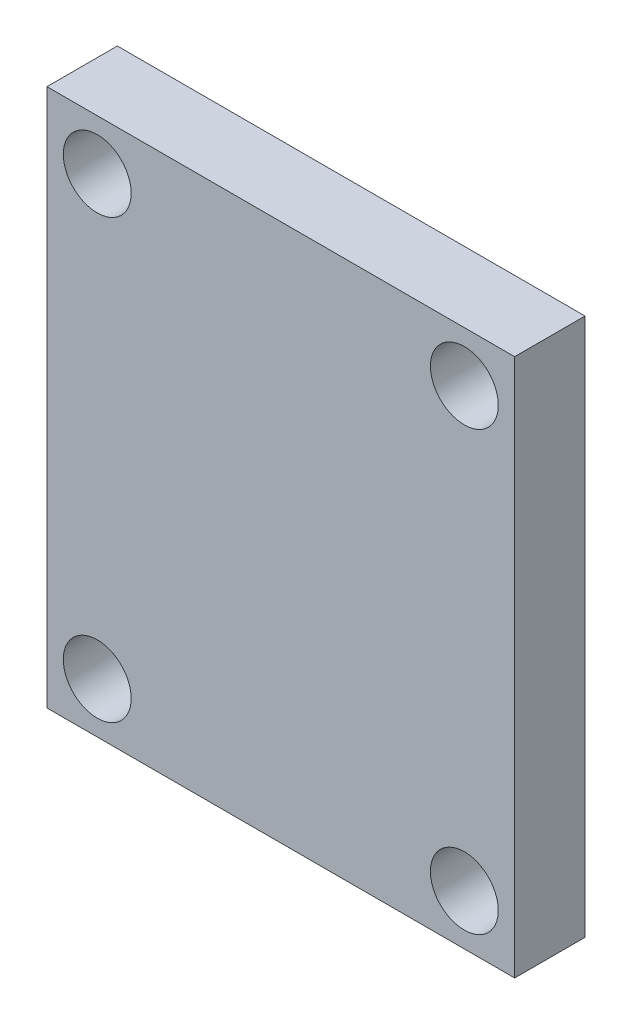
SolidWorks part; units mm, degrees
ref_plane "Přední rovina" through (0, 0, 0) normal (0, 0, 1) x (1, 0, 0)
ref_plane "Horní rovina" through (0, 0, 0) normal (0, 1, 0) x (1, 0, 0)
ref_plane "Pravá rovina" through (0, 0, 0) normal (1, 0, 0) x (0, 0, -1)
sketch "Skica1" plane through (0, 0, 0) normal (0, 0, 1) x (1, 0, 0)
  line L14 (-46.5, -53.5) -> (46.5, -53.5)
  line L15 (-46.5, -53.5) -> (-46.5, 53.5)
  line L16 (-46.5, 53.5) -> (46.5, 53.5)
  line L17 (46.5, -53.5) -> (46.5, 53.5)
  line L18 (-46.5, -53.5) -> (46.5, 53.5) construction
  line L19 (-46.5, 53.5) -> (46.5, -53.5) construction
  point P3 (0, 0)
  dimension "D1" = 107
  dimension "D2" = 93
extrude "Přidat vysunutím1" add sketch "Skica1" along normal blind 14
sketch "Skica2" plane through (0, 0, 0) normal (0, 0, -1) x (-1, 0, 0)
  line L0 (0, 43.5) -> (0, -70.4303) construction
  line L1 (-59.3322, 0) -> (56.1308, 0) construction
  line L2 (46.5, -53.5) -> (-46.5, -53.5) construction
  line L3 (46.5, 53.5) -> (46.5, -53.5) construction
  line L6 (-46.5, 53.5) -> (46.5, 53.5) construction
  circle A0 centre (-36.5, 43.5) radius 6.75
  circle A1 centre (36.5, 43.5) radius 6.75
  circle A2 centre (36.5, -43.5) radius 6.75
  circle A3 centre (-36.5, -43.5) radius 6.75
  dimension "D8" = 13.5
  dimension "D9" = 13.5
  dimension "D10" = 13.5
  dimension "D11" = 13.5
  dimension "D12" = 10
  dimension "D13" = 10
  dimension "D2" = 10
  dimension "D3" = 87
  dimension "D4" = 73
  dimension "D5" = 10
  dimension "D6" = 10
  dimension "D7" = 73
extrude "Odebrat vysunutím1" cut sketch "Skica2" against normal through all
sketch "Skica4" plane through (0, 0, 0) normal (0, 0, -1) x (-1, 0, 0)
  line L1 (-37.5, -26.5) -> (37.5, -26.5)
  line L2 (-37.5, -26.5) -> (-37.5, 26.5)
  line L3 (-37.5, 26.5) -> (37.5, 26.5)
  line L4 (37.5, -26.5) -> (37.5, 26.5)
  line L5 (-37.5, -26.5) -> (37.5, 26.5) construction
  line L6 (-37.5, 26.5) -> (37.5, -26.5) construction
  point P0 (0, 0)
  dimension "D1" = 75
  dimension "D2" = 53
extrude "Odebrat vysunutím2" cut sketch "Skica4" against normal blind 0.0001
